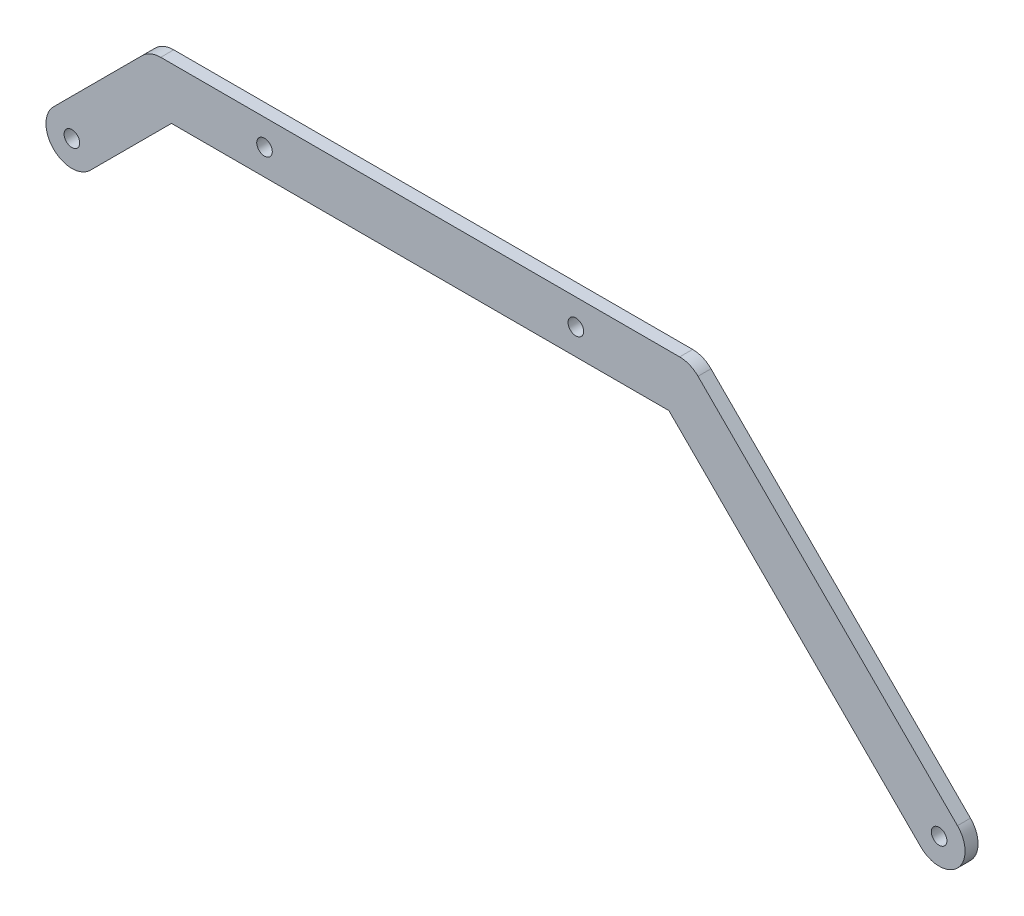
SolidWorks part; units mm, degrees
ref_plane "Front Plane" through (0, 0, 0) normal (0, 0, 1) x (1, 0, 0)
ref_plane "Top Plane" through (0, 0, 0) normal (0, 1, 0) x (1, 0, 0)
ref_plane "Right Plane" through (0, 0, 0) normal (1, 0, 0) x (0, 0, -1)
sketch "Sketch1" plane through (0, 0, 0) normal (0, 0, 1) x (1, 0, 0)
  line L6 (-195.8579, -10) -> (-227.1619, -41.304)
  line L7 (100, -100) -> (-321.4488, -100)
  line L8 (-207.0711, 7.0711) -> (-241.304, -27.1619)
  line L10 (-200, 10) -> (0, 10)
  line L11 (-195.8579, -10) -> (-4.1421, -10)
  line L13 (7.0711, 7.0711) -> (107.0711, -92.9289)
  line L14 (-4.1421, -10) -> (92.9289, -107.0711)
  arc A1 (-241.304, -27.1619) -> (-227.1619, -41.304) centre (-234.2329, -34.2329) ccw
  arc A2 (-200, 10) -> (-207.0711, 7.0711) centre (-200, 0) ccw
  arc A4 (7.0711, 7.0711) -> (0, 10) centre (0, 0) ccw
  arc A5 (92.9289, -107.0711) -> (107.0711, -92.9289) centre (100, -100) ccw
  arc A6 (-200, 10) -> (-207.0711, 7.0711) centre (-200, 0) ccw
  circle A7 centre (-234.2329, -34.2329) radius 3
  arc A8 (7.0711, 7.0711) -> (0, 10) centre (0, 0) ccw
  circle A9 centre (100, -100) radius 3
  circle A10 centre (-160, 0) radius 3
  circle A11 centre (-40, 0) radius 3
  point P2 (-217.1165, -17.1165)
  point P11 (-100, 0)
  point P17 (50, -50)
  point P23 (-241.304, -41.304)
  dimension "D6" = 6
  dimension "D8" = 6
  dimension "D11" = 6
  dimension "D12" = 6
  dimension "D1" = 200
  dimension "D2" = 10
  dimension "D3" = 90
  dimension "D4" = 10
  dimension "D5" = 10
  dimension "D7" = 100
extrude "Boss-Extrude2" add sketch "Sketch1" along normal blind 5
